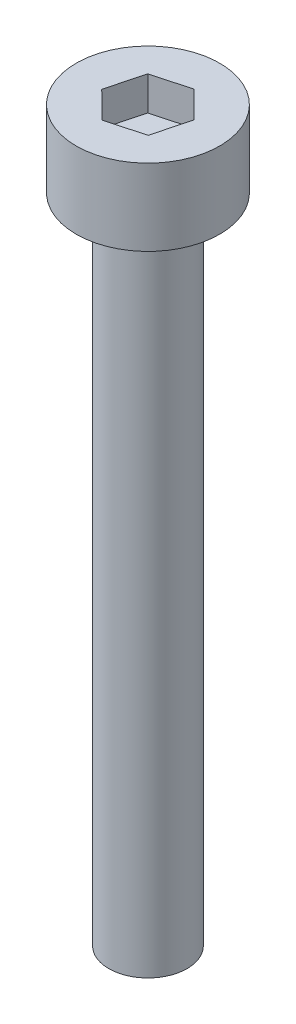
SolidWorks part; units mm, degrees
ref_plane "前视基准面" through (0, 0, 0) normal (0, 0, 1) x (1, 0, 0)
ref_plane "上视基准面" through (0, 0, 0) normal (0, 1, 0) x (1, 0, 0)
ref_plane "右视基准面" through (0, 0, 0) normal (1, 0, 0) x (0, 0, -1)
sketch "草图1" plane through (0, 0, 0) normal (0, 1, 0) x (1, 0, 0)
  circle A0 centre (0, 0) radius 1.5
  dimension "D1" = 3
extrude "凸台-拉伸1" add sketch "草图1" along normal blind 25
sketch "草图2" plane through (0, 25, 0) normal (0, 1, 0) x (1, 0, 0)
  circle A0 centre (0, 0) radius 2.75
  dimension "D1" = 5.5
extrude "凸台-拉伸2" add sketch "草图2" along normal blind 2.93
sketch "草图3" plane through (0, 27.93, 0) normal (0, 1, 0) x (1, 0, 0)
  line L1 (1.024, -1.0172) -> (1.3929, 0.3782)
  line L2 (1.3929, 0.3782) -> (0.3689, 1.3954)
  line L3 (0.3689, 1.3954) -> (-1.024, 1.0172)
  line L4 (-1.024, 1.0172) -> (-1.3929, -0.3782)
  line L5 (-1.3929, -0.3782) -> (-0.3689, -1.3954)
  line L6 (-0.3689, -1.3954) -> (1.024, -1.0172)
  circle A0 centre (0, 0) radius 1.25 construction
  dimension "D1" = 2.5
extrude "切除-拉伸1" cut sketch "草图3" against normal blind 1.3
